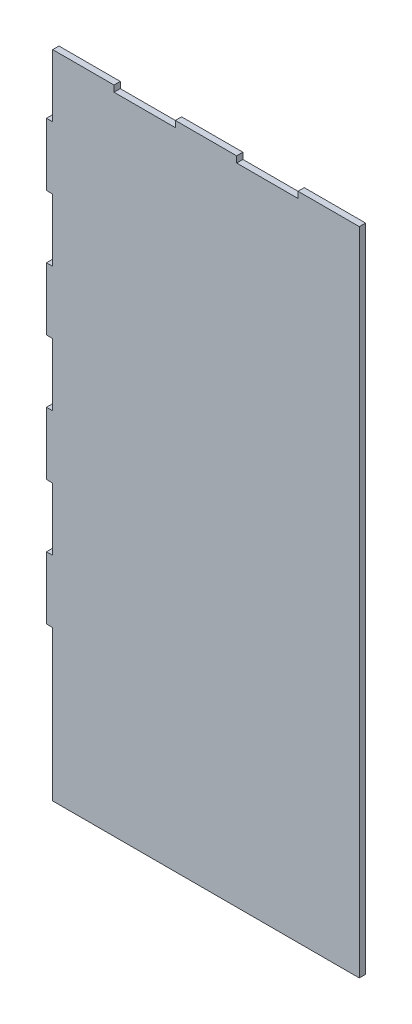
SolidWorks part; units mm, degrees
material "PMMA"
ref_plane "Plan de face" through (0, 0, 0) normal (0, 0, 1) x (1, 0, 0)
ref_plane "Plan de dessus" through (0, 0, 0) normal (0, 1, 0) x (1, 0, 0)
ref_plane "Plan de droite" through (0, 0, 0) normal (1, 0, 0) x (0, 0, -1)
sketch "Esquisse1" plane through (0, 0, 0) normal (0, 0, 1) x (1, 0, 0)
  line L0 (0, 120) -> (0, 170)
  line L1 (0, 170) -> (5, 170)
  line L2 (5, 170) -> (5, 220)
  line L3 (5, 220) -> (0, 220)
  line L4 (0, 220) -> (0, 270)
  line L5 (0, 270) -> (5, 270)
  line L6 (5, 270) -> (5, 320)
  line L7 (5, 320) -> (0, 320)
  line L8 (0, 320) -> (0, 370)
  line L9 (0, 370) -> (5, 370)
  line L10 (5, 370) -> (5, 420)
  line L11 (5, 420) -> (0, 420)
  line L12 (0, 420) -> (0, 470)
  line L13 (0, 470) -> (5, 470)
  line L14 (5, 470) -> (5, 520)
  line L15 (5, 520) -> (54, 520)
  line L16 (54, 520) -> (54, 515)
  line L17 (54, 515) -> (103, 515)
  line L18 (103, 515) -> (103, 520)
  line L19 (103, 520) -> (152, 520)
  line L20 (152, 520) -> (152, 515)
  line L21 (152, 515) -> (201, 515)
  line L22 (201, 515) -> (201, 520)
  line L23 (201, 520) -> (250, 520)
  line L39 (250, 0) -> (5, 0)
  line L42 (250, 0) -> (250, 520)
  line L43 (0, 120) -> (5, 120)
  line L44 (5, 120) -> (5, 0)
  dimension "D1" = 120
  dimension "D2" = 250
  dimension "D3" = 50
  dimension "D4" = 5
  dimension "D5" = 5
  dimension "D6" = 49
  dimension "D8" = 520
extrude "Boss.-Extru.1" add sketch "Esquisse1" along normal blind 5
